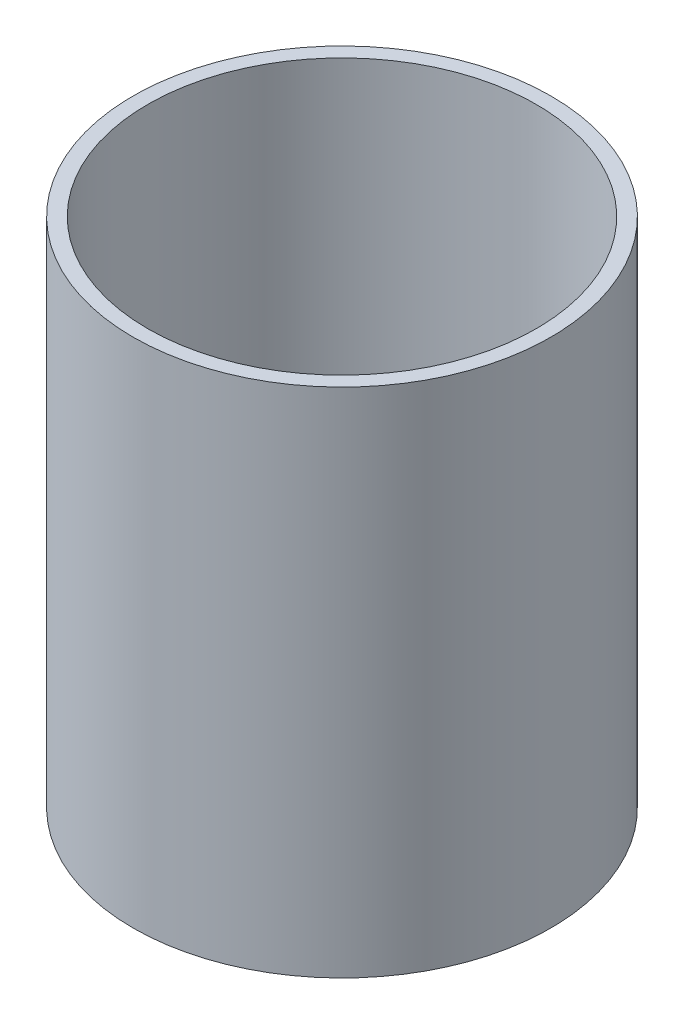
SolidWorks part; units mm, degrees
ref_plane "Plano frontal" through (0, 0, 0) normal (0, 0, 1) x (1, 0, 0)
ref_plane "Plano superior" through (0, 0, 0) normal (0, 1, 0) x (1, 0, 0)
ref_plane "Plano direito" through (0, 0, 0) normal (1, 0, 0) x (0, 0, -1)
sketch "Esboço1" plane through (0, 0, 0) normal (0, 1, 0) x (1, 0, 0)
  circle A0 centre (0, 0) radius 57.15
  circle A1 centre (0, 0) radius 53.15
extrude "Ressalto-extrusão1" add sketch "Esboço1" along normal blind 140
